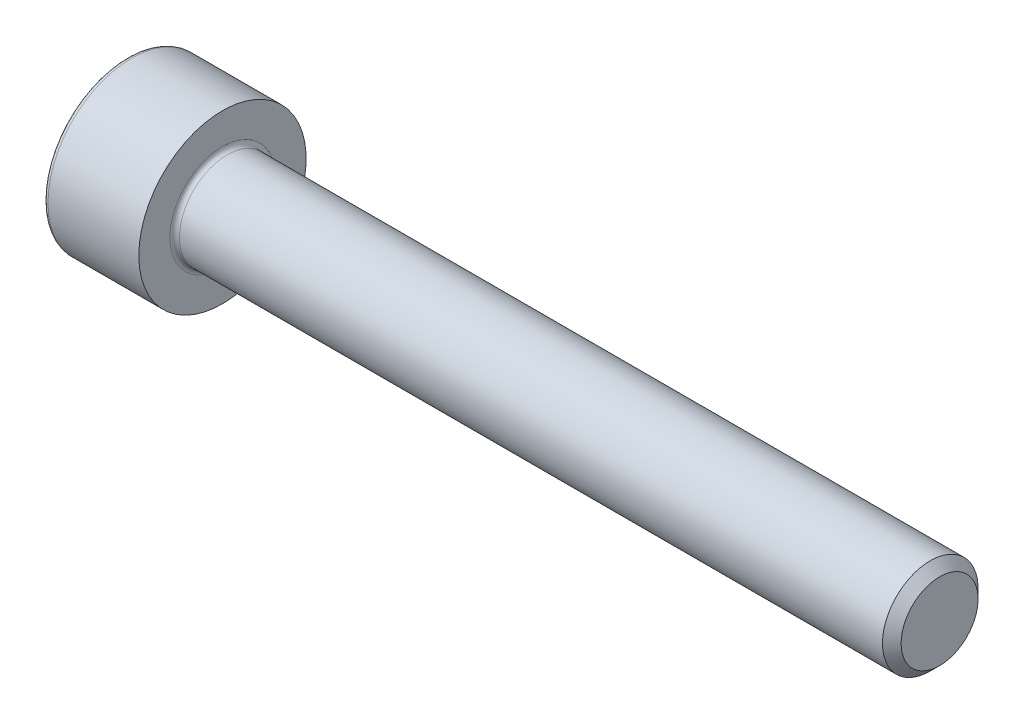
SolidWorks part; units mm, degrees
ref_plane "Plane1" through (0, 0, 0) normal (0, 0, 1) x (1, 0, 0)
ref_plane "Plane2" through (0, 0, 0) normal (0, 1, 0) x (1, 0, 0)
ref_plane "Plane3" through (0, 0, 0) normal (1, 0, 0) x (0, 0, -1)
sketch "BodySke" plane through (0, 0, 0) normal (0, 0, 1) x (1, 0, 0)
  line L0 (0, 0) -> (0, 3.5)
  line L1 (0, 3.5) -> (4, 3.5)
  line L2 (4, 3.5) -> (4, 2)
  line L3 (4, 2) -> (33.61, 2)
  line L4 (34, 1.61) -> (34, 0)
  line L5 (34, 0) -> (0, 0)
  line L6 (-31.75, 0) -> (127, 0) construction
  line L8 (34, 1.61) -> (33.61, 2)
  line L10 (34, -1.61) -> (33.61, -2) construction
  line L11 (4.7, 9.525) -> (4.7, 3.175) construction
  line L12 (14, 9.525) -> (14, 3.175) construction
  line L13 (-26, 9.525) -> (-26, 3.175) construction
  dimension "Diameter" = 4
  dimension "Head_ht" = 4
  dimension "Length" = 30
  dimension "Body_ch_ang" = 45
  dimension "Head_dia" = 7
  dimension "Minor_dia" = 3.22
  dimension "Advance" = 0.7
  dimension "Thread_nom" = 20
  dimension "Thread_length" = 60
revolve "Base-Revolve" add sketch "BodySke"
cosmetic thread "ThreadCosmetic"
fillet "Fillet1" radius 0.2 1 edges at (4, 0, 2)
fillet "Fillet2" radius 0.2 1 edges at (0, 0, 3.5)
sketch "Sketch2" plane through (0, 0, 0) normal (0, 0, 1) x (1, 0, 0)
  line L0 (0, 1.5355) -> (2, 1.5355)
  line L1 (2, 1.5355) -> (2.8865, 0)
  line L2 (-31.75, 0) -> (127, 0) construction
  line L3 (2.8865, 0) -> (0, 0)
  line L4 (0, 0) -> (0, 1.5355)
  line L6 (0, 0) -> (47.625, 0) construction
  dimension "D1" = 1.5355
  dimension "D2" = 60
  dimension "Depth" = 2
revolve "Hex-PreBroach" cut sketch "Sketch2" angle 360 about L6
sketch "Sketch3" plane through (0, 0, 0) normal (-1, 0, 0) x (0, 0.5, 0.866)
  line L0 (0.8865, 1.5355) -> (-0.8865, 1.5355)
  line L1 (-0.8865, 1.5355) -> (-1.773, 0)
  line L2 (0.8865, 1.5355) -> (1.773, 0)
  line L3 (0.8865, -1.5355) -> (1.773, 0)
  line L4 (0.8865, -1.5355) -> (-0.8865, -1.5355)
  line L5 (-0.8865, -1.5355) -> (-1.773, 0)
  dimension "D1" = 1.5355
  dimension "D2" = 1.5355
  dimension "Hex_size" = 3.071
extrude "Hex" cut sketch "Sketch3" against normal blind 2
sketch "ThdSchSke" plane through (0, 0, 0) normal (0, 0, 1) x (1, 0, 0)
  line L0 (14, -1.61) -> (13.7269, -2)
  line L1 (14, -1.61) -> (14.2731, -2)
  line L2 (14.2731, -2) -> (14.2731, -2.5)
  line L3 (-3.175, 0) -> (5.1513, 0) construction
  line L4 (0, 3.3) -> (0, -3.3) construction
  line L5 (14.2731, -2.5) -> (13.7269, -2.5)
  line L6 (13.7269, -2.5) -> (13.7269, -2)
  dimension "Thread_minor" = 3.22
  dimension "Diameter" = 4
  dimension "Start" = 14
  dimension "SideAngle" = 55
  dimension "VeeAngle" = 70
  dimension "Overcut" = 5
revolve "ThreadSchematic" [suppressed] cut sketch "ThdSchSke" angle 360 about L3
pattern_linear "ThdSchPat" [suppressed]
equation "\"D2@Sketch3\" = \"Hex_size@Sketch3\" / 2"
equation "\"D1@Sketch3\" = \"Hex_size@Sketch3\" / 2"
equation "\"D1@Sketch2\" = \"Hex_size@Sketch3\" / 2"
equation "\"Thread_minor@ThreadCosmetic\"  =  \"Minor_dia@BodySke\""
equation "\"Depth@Sketch2\" =  \"Key_eng@Hex\""
equation "\"Thread_length@ThreadCosmetic\" = ((sgn( (\"Length@BodySke\" - \"Advance@BodySke\" * 3.0) - \"Thread_nom@BodySke\" )-1)*( (\"Length@BodySke\" - \"Advance@BodySke\" * 3.0) - \"Thread_nom@BodySke\" ))/-2+ \"Thread_nom@BodySke\""
equation "\"Thread_minor@ThdSchSke\" = \"Minor_dia@BodySke\""
equation "\"Diameter@ThdSchSke\" = \"Diameter@BodySke\""
equation "\"Overcut@ThdSchSke\" = \"Diameter@BodySke\" * 1.25"
equation "\"Start@ThdSchSke\" = \"Head_ht@BodySke\" + \"Length@BodySke\" - \"Thread_length@ThreadCosmetic\"  '---Non-countersunk---"
equation "\"Num_threads@ThdSchPat\" = int( \"Thread_length@ThreadCosmetic\" / \"Advance@BodySke\" + 0.999 )  + 1"
equation "\"Advance@ThdSchPat\" = \"Thread_length@ThreadCosmetic\" /  (\"Num_threads@ThdSchPat\" - 1) 'relax it"
equation "\"Num_threads@ThdSchPat\" = \"Num_threads@ThdSchPat\" - sgn( \"Num_threads@ThdSchPat\" - 1) '---chamfered tips only---"
